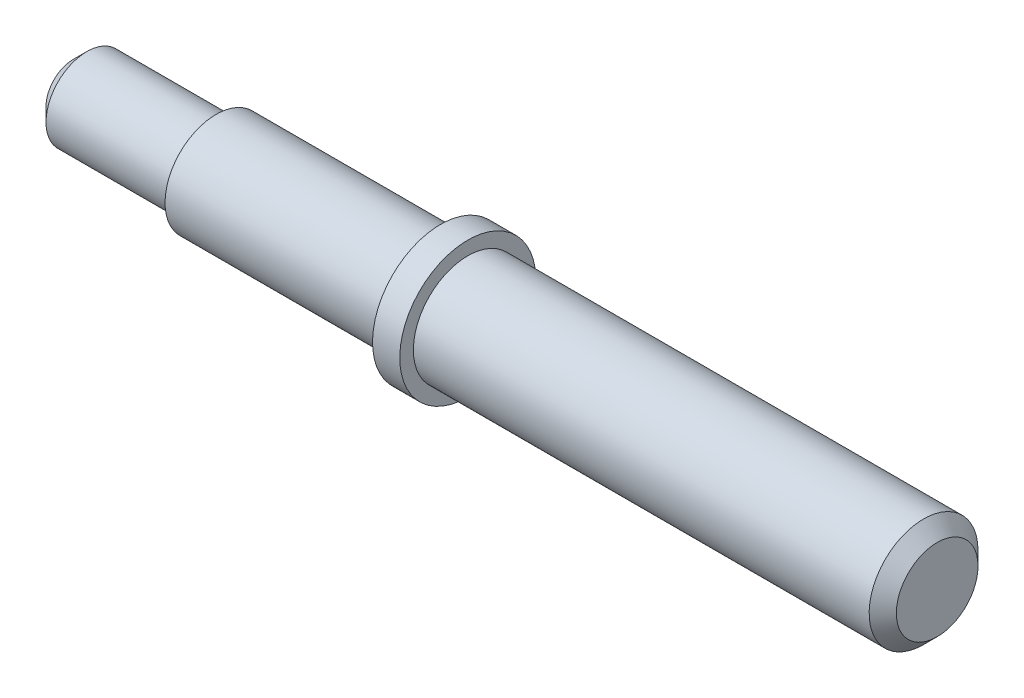
SolidWorks part; units mm, degrees
ref_plane "Ebene vorne" through (0, 0, 0) normal (0, 0, 1) x (1, 0, 0)
ref_plane "Ebene oben" through (0, 0, 0) normal (0, 1, 0) x (1, 0, 0)
ref_plane "Ebene rechts" through (0, 0, 0) normal (1, 0, 0) x (0, 0, -1)
sketch "Skizze1" plane through (0, 0, 0) normal (0, 0, 1) x (1, 0, 0)
  line L0 (0, 0) -> (-69, 0)
  line L1 (-69, 0) -> (-69, -2)
  line L2 (-69, -2) -> (-73, -2)
  line L3 (-73, -2) -> (-73, 0.5)
  line L4 (-73, 0.5) -> (-127, 0.5)
  line L5 (-127, 0.5) -> (-127, 8)
  line L6 (-127, 8) -> (0, 8)
  line L7 (0, 8) -> (0, 0)
  dimension "D1" = 69
  dimension "D2" = 8
  dimension "D3" = 10
  dimension "D4" = 4
  dimension "D5" = 54
  dimension "D6" = 7.5
revolve "Rotation1" add sketch "Skizze1" angle 360 about L6
cosmetic thread "Gewindedarstellung2" parameters "D1"=18, "D2"=13.797
sketch "Skizze2" plane through (-127, 0, 0) normal (-1, 0, 0) x (0, 0, 1)
  circle A0 centre (0, 8) radius 6
  circle A1 centre (0, 8) radius 7.5
  dimension "D1" = 12
extrude "Schnitt-Linear austragen2" cut sketch "Skizze2" against normal blind 21
cosmetic thread "Gewindedarstellung1" parameters "D1"=20, "D2"=10.072
chamfer "Fase2" distance 2 angle 45 1 edges at (-127, 2, 0)
sketch "Skizze3" plane through (-69, 0, 0) normal (1, 0, 0) x (0, 0, -1)
  circle A0 centre (0, 8) radius 10
chamfer "Fase3" distance 2 angle 45 1 edges at (0, 0, 0)
